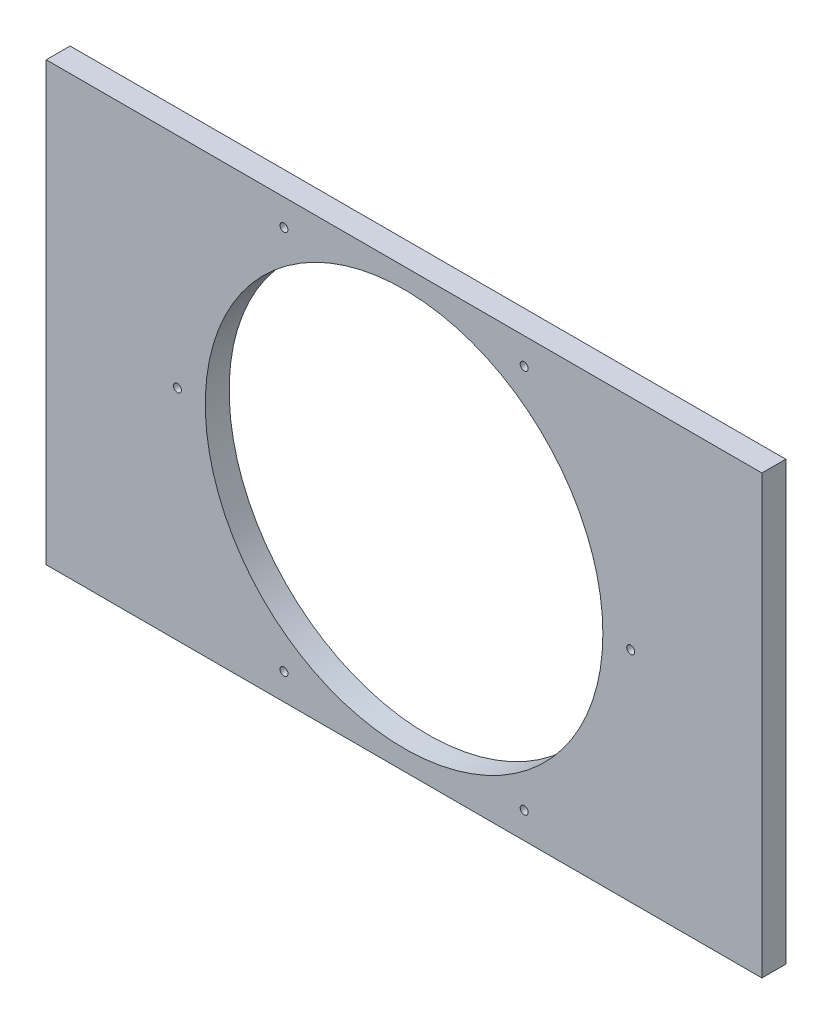
SolidWorks part; units mm, degrees
ref_plane "Front Plane" through (0, 0, 0) normal (0, 0, 1) x (1, 0, 0)
ref_plane "Top Plane" through (0, 0, 0) normal (0, 1, 0) x (1, 0, 0)
ref_plane "Right Plane" through (0, 0, 0) normal (1, 0, 0) x (0, 0, -1)
sketch "Sketch1" plane through (0, 0, 0) normal (0, 0, 1) x (1, 0, 0)
  line L1 (0, 0) -> (180, 0)
  line L2 (0, 0) -> (0, 110)
  line L3 (0, 110) -> (180, 110)
  line L4 (180, 0) -> (180, 110)
sketch "Sketch2" plane through (0, 0, 0) normal (0, 0, 1) x (1, 0, 0)
  circle A0 centre (90, 55) radius 50
extrude "Boss-Extrude1" add sketch "Sketch1" along normal blind 6 contours L3 L4 L1 L2
extrude "Cut-Extrude1" cut sketch "Sketch2" along normal blind 6
ref_plane "Plane1" through (0, 0, 6) normal (0, 0, 1) x (1, 0, 0)
sketch "Sketch3" plane through (0, 0, 6) normal (0, 0, 1) x (1, 0, 0)
  point P0 (90, 55)
sketch "Sketch4" plane through (0, 0, 0) normal (0, 0, 1) x (1, 0, 0)
  line L0 (33, 55) -> (147, 55) construction
  line L1 (59.7946, 6.6613) -> (120.2054, 103.3387) construction
  line L2 (59.7946, 103.3387) -> (120.2054, 6.6613) construction
  circle A0 centre (59.7946, 103.3387) radius 1
  circle A1 centre (120.2054, 103.3387) radius 1
  circle A2 centre (147, 55) radius 1
  circle A3 centre (120.2054, 6.6613) radius 1
  circle A4 centre (59.7946, 6.6613) radius 1
  circle A5 centre (33, 55) radius 1
  point P4 (90, 55)
  point P9 (90, 55)
  point P12 (90, 55)
extrude "Cut-Extrude2" cut sketch "Sketch4" along normal blind 40
